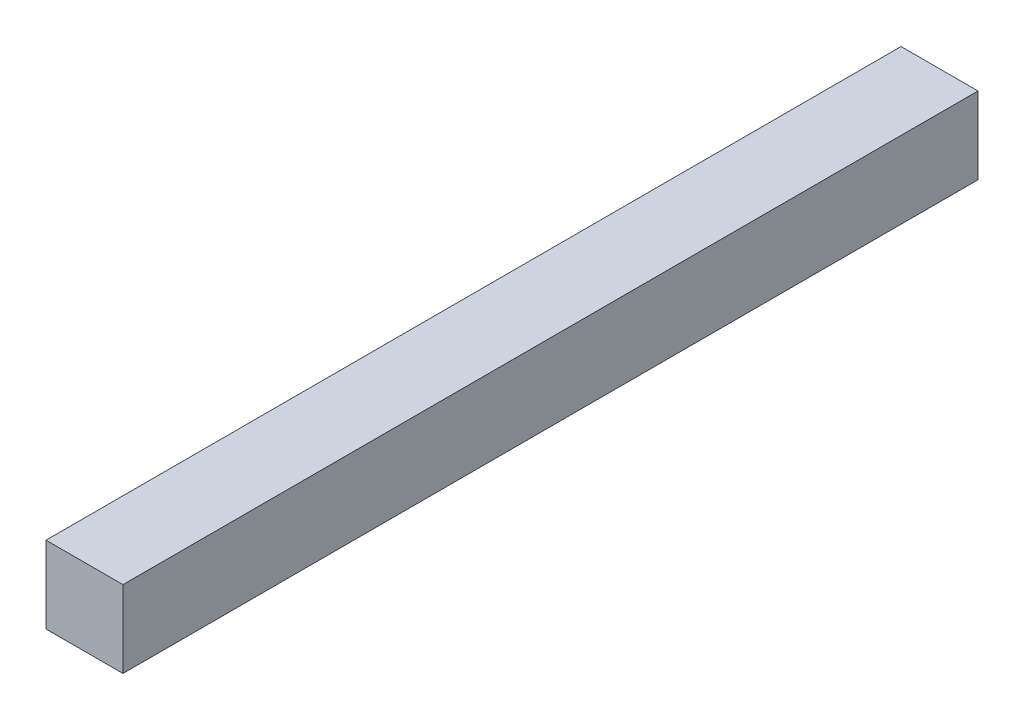
SolidWorks part; units mm, degrees
ref_plane "Face" through (0, 0, 0) normal (0, 0, 1) x (1, 0, 0)
ref_plane "Dessus" through (0, 0, 0) normal (0, 1, 0) x (1, 0, 0)
ref_plane "Droite" through (0, 0, 0) normal (1, 0, 0) x (0, 0, -1)
sketch "Esquisse1" plane through (0, 0, 0) normal (0, 0, 1) x (1, 0, 0)
  line L1 (0, 0) -> (18, 0)
  line L2 (0, 0) -> (0, 18)
  line L3 (0, 18) -> (18, 18)
  line L4 (18, 0) -> (18, 18)
  dimension "D1" = 18
  dimension "D2" = 18
extrude "Extrusion1" add sketch "Esquisse1" against normal blind 200
